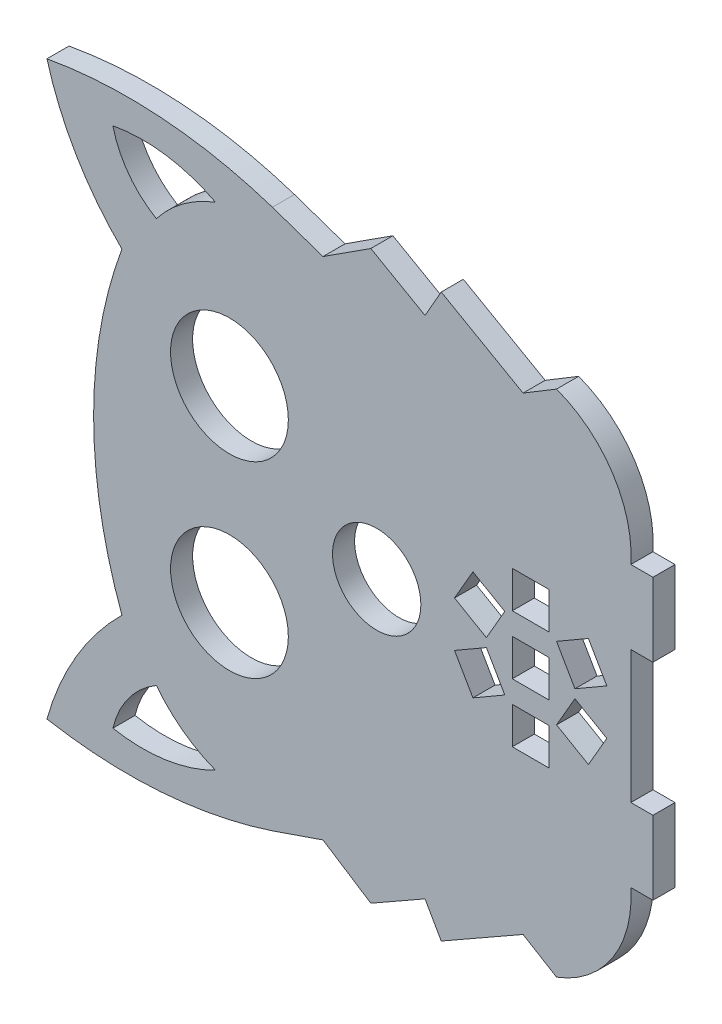
SolidWorks part; units mm, degrees
ref_plane "Front Plane" through (0, 0, 0) normal (0, 0, 1) x (1, 0, 0)
ref_plane "Top Plane" through (0, 0, 0) normal (0, 1, 0) x (1, 0, 0)
ref_plane "Right Plane" through (0, 0, 0) normal (1, 0, 0) x (0, 0, -1)
sketch "Sketch2" plane through (0, 0, 0) normal (0, 0, 1) x (1, 0, 0)
  line L0 (81.0321, 50.1813) -> (81.0321, 60.1813)
  line L1 (81.0321, 60.1813) -> (78.0321, 60.1813)
  line L16 (78.0321, 22.1813) -> (81.0321, 22.1813)
  line L17 (81.0321, 22.1813) -> (81.0321, 32.1813)
  line L18 (81.0321, 32.1813) -> (78.0321, 32.1813)
  line L19 (78.0321, 32.1813) -> (78.0321, 50.1813)
  line L20 (78.0321, 50.1813) -> (81.0321, 50.1813)
  line L21 (61.923, 43.6813) -> (61.923, 38.6813)
  line L22 (61.923, 38.6813) -> (66.923, 38.6813)
  line L23 (66.923, 38.6813) -> (66.923, 43.6813)
  line L24 (66.923, 43.6813) -> (61.923, 43.6813)
  line L25 (61.923, 35.6813) -> (61.923, 30.6813)
  line L26 (61.923, 30.6813) -> (66.923, 30.6813)
  line L27 (66.923, 30.6813) -> (66.923, 35.6813)
  line L28 (66.923, 35.6813) -> (61.923, 35.6813)
  line L29 (72.2663, 48.5964) -> (67.9362, 46.0964)
  line L30 (67.9362, 46.0964) -> (70.4362, 41.7662)
  line L31 (70.4362, 41.7662) -> (74.7663, 44.2662)
  line L32 (74.7663, 44.2662) -> (72.2663, 48.5964)
  line L33 (67.9362, 36.2662) -> (72.2663, 33.7662)
  line L34 (72.2663, 33.7662) -> (74.7663, 38.0964)
  line L35 (74.7663, 38.0964) -> (70.4362, 40.5964)
  line L36 (70.4362, 40.5964) -> (67.9362, 36.2662)
  line L37 (61.923, 51.6813) -> (61.923, 46.6813)
  line L38 (61.923, 46.6813) -> (66.923, 46.6813)
  line L39 (66.923, 46.6813) -> (66.923, 51.6813)
  line L40 (66.923, 51.6813) -> (61.923, 51.6813)
  line L41 (56.5798, 33.7662) -> (60.9099, 36.2662)
  line L42 (60.9099, 36.2662) -> (58.4099, 40.5964)
  line L43 (58.4099, 40.5964) -> (54.0798, 38.0964)
  line L44 (54.0798, 38.0964) -> (56.5798, 33.7662)
  line L45 (60.9099, 46.0964) -> (56.5798, 48.5964)
  line L46 (56.5798, 48.5964) -> (54.0798, 44.2662)
  line L47 (54.0798, 44.2662) -> (58.4099, 41.7662)
  line L48 (58.4099, 41.7662) -> (60.9099, 46.0964)
  line L49 (78.0321, 41.1813) -> (23.507, 41.1813) construction
  line L50 (29.3426, 77.8618) -> (36.2125, 75.4953)
  line L51 (36.2125, 75.4953) -> (42.71, 79.6915)
  line L52 (42.71, 79.6915) -> (50.0742, 75.4953)
  line L53 (50.0742, 75.4953) -> (52.2746, 79.3569)
  line L54 (52.2746, 79.3569) -> (63.3891, 73.0238)
  line L55 (63.3891, 73.0238) -> (67.9362, 75.7701)
  line L56 (63.3891, 9.3388) -> (67.9362, 6.5926)
  line L57 (52.2746, 3.0057) -> (63.3891, 9.3388)
  line L58 (50.0742, 6.8674) -> (52.2746, 3.0057)
  line L59 (42.71, 2.6711) -> (50.0742, 6.8674)
  line L60 (36.2125, 6.8674) -> (42.71, 2.6711)
  line L61 (29.3426, 4.5008) -> (36.2125, 6.8674)
  circle A0 centre (23.507, 53.9313) radius 8
  circle A1 centre (43.507, 41.1813) radius 6
  circle A2 centre (23.507, 28.4313) radius 8
  arc A34 (29.3426, 77.8618) -> (-1.2792, 80.0172) centre (9.7799, 18.5334) ccw
  arc A35 (-1.2792, 80.0172) -> (8.9024, 62.7188) centre (36.2125, 90.4388) ccw
  arc A36 (8.9024, 62.7188) -> (8.9024, 19.6438) centre (67.2985, 41.1813) ccw
  arc A37 (29.3426, 4.5008) -> (-1.2792, 2.3455) centre (9.7799, 63.8292) cw
  arc A38 (-1.2792, 2.3455) -> (8.9024, 19.6438) centre (36.2125, -8.0762) cw
  arc A39 (21.6117, 74.5865) -> (7.6783, 76.612) centre (11.7046, 55.3732) ccw
  arc A40 (7.6783, 76.612) -> (13.5809, 68.637) centre (19.9373, 79.5135) ccw
  arc A41 (13.5809, 68.637) -> (21.6117, 74.5865) centre (28.1138, 57.4149) cw
  arc A42 (7.6783, 5.7506) -> (13.5809, 13.7256) centre (19.9373, 2.8491) cw
  arc A43 (13.5809, 13.7256) -> (21.6117, 7.7761) centre (28.1138, 24.9477) ccw
  arc A44 (21.6117, 7.7761) -> (7.6783, 5.7506) centre (11.7046, 26.9895) cw
  arc A45 (67.9362, 75.7701) -> (78.0321, 60.1813) centre (62.5267, 61.203) cw
  arc A46 (67.9362, 6.5926) -> (78.0321, 22.1813) centre (62.5267, 21.1596) ccw
  dimension "D2" = 12.75
  dimension "D3" = 12.75
extrude "Boss-Extrude1" add sketch "Sketch2" along normal blind 3
